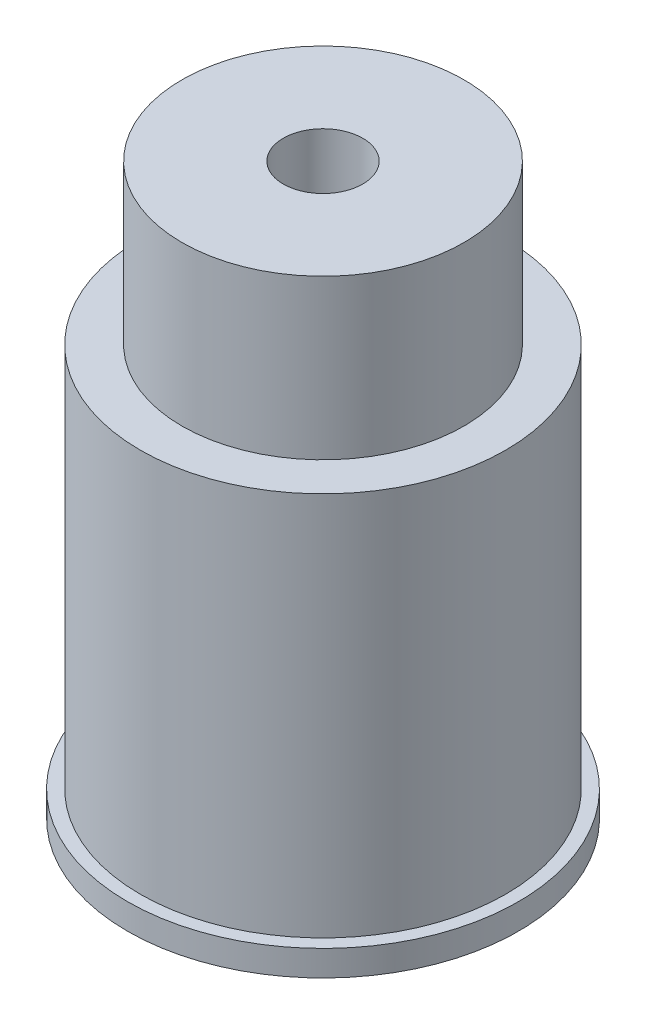
SolidWorks part; units mm, degrees
ref_plane "Front Plane" through (0, 0, 0) normal (0, 0, 1) x (1, 0, 0)
ref_plane "Top Plane" through (0, 0, 0) normal (0, 1, 0) x (1, 0, 0)
ref_plane "Right Plane" through (0, 0, 0) normal (1, 0, 0) x (0, 0, -1)
sketch "Sketch2" plane through (0, 0, 0) normal (0, 1, 0) x (1, 0, 0)
  circle A0 centre (0, 0) radius 7.625
  dimension "D1" = 15.25
extrude "Boss-Extrude1" add sketch "Sketch2" along normal blind 1
sketch "Sketch4" plane through (0, 1, 0) normal (0, 1, 0) x (1, 0, 0)
  circle A0 centre (0, 0) radius 7.125
  dimension "D1" = 14.25
extrude "Boss-Extrude2" add sketch "Sketch4" along normal blind 15
sketch "Sketch5" plane through (0, 16, 0) normal (0, 1, 0) x (1, 0, 0)
  circle A0 centre (0, 0) radius 5.5
  dimension "D1" = 11
extrude "Boss-Extrude3" add sketch "Sketch5" along normal blind 6.2
sketch "Sketch6" plane through (0, 22.2, 0) normal (0, 1, 0) x (1, 0, 0)
  circle A0 centre (0, 0) radius 1.55
  dimension "D1" = 3.1
extrude "Cut-Extrude1" cut sketch "Sketch6" against normal through all
